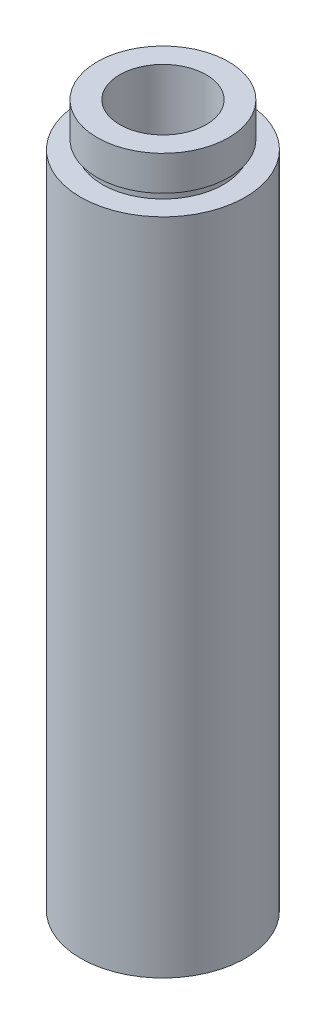
SolidWorks part; units mm, degrees
ref_plane "前视基准面" through (0, 0, 0) normal (0, 0, 1) x (1, 0, 0)
ref_plane "上视基准面" through (0, 0, 0) normal (0, 1, 0) x (1, 0, 0)
ref_plane "右视基准面" through (0, 0, 0) normal (1, 0, 0) x (0, 0, -1)
sketch "草图1" plane through (0, 0, 0) normal (0, 0, 1) x (1, 0, 0)
  line L0 (0, 161.3762) -> (0, 0) construction
  line L1 (141.7365, 0) -> (-131.7984, 0) construction
  line L2 (7, 0) -> (7, 4.5)
  line L3 (7.6, 4.5) -> (7.6, 5.5)
  line L4 (7, 4.5) -> (7.6, 4.5)
  line L5 (5, 5.5) -> (5, 81.2)
  line L6 (7.6, 5.5) -> (5, 5.5)
  line L7 (9.525, 0) -> (9.525, 76.2)
  line L8 (7, 0) -> (9.525, 0)
  line L9 (7, 76.2) -> (7, 77.2)
  line L10 (9.525, 76.2) -> (7, 76.2)
  line L11 (7.6, 77.2) -> (7.6, 81.2)
  line L12 (7, 77.2) -> (7.6, 77.2)
  line L13 (7.6, 81.2) -> (5, 81.2)
  dimension "D1" = 7
  dimension "D2" = 4.5
  dimension "D3" = 7.6
  dimension "D4" = 5
  dimension "D5" = 7
  dimension "D6" = 7.6
  dimension "D7" = 5
  dimension "D8" = 1
  dimension "D9" = 9.525
  dimension "D10" = 1
  dimension "D11" = 76.2
revolve "旋转1" add sketch "草图1" angle 360 about L0
cosmetic thread "装饰螺纹线1" parameters "D2"=15
cosmetic thread "装饰螺纹线2" parameters "D2"=11
cosmetic thread "装饰螺纹线3" parameters "D2"=15
